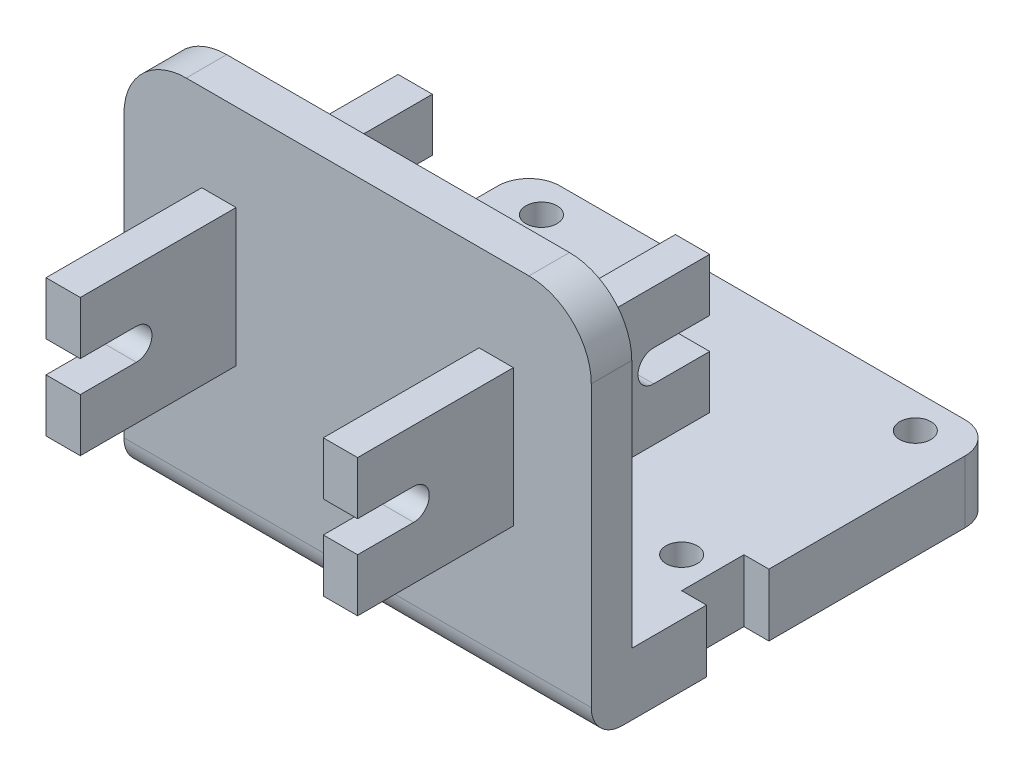
SolidWorks part; units mm, degrees
ref_plane "Front Plane" through (0, 0, 0) normal (0, 0, 1) x (1, 0, 0)
ref_plane "Top Plane" through (0, 0, 0) normal (0, 1, 0) x (1, 0, 0)
ref_plane "Right Plane" through (0, 0, 0) normal (1, 0, 0) x (0, 0, -1)
sketch "Sketch1" plane through (0, 0, 0) normal (0, 1, 0) x (1, 0, 0)
  line L1 (-37.5, -27.5) -> (37.5, -27.5)
  line L2 (-37.5, -27.5) -> (-37.5, 27.5)
  line L3 (-37.5, 27.5) -> (37.5, 27.5)
  line L4 (37.5, -27.5) -> (37.5, 27.5)
  line L5 (-37.5, -27.5) -> (37.5, 27.5) construction
  line L6 (-37.5, 27.5) -> (37.5, -27.5) construction
  circle A0 centre (-30, 22) radius 2.5
  circle A1 centre (30, 22) radius 2.5
  circle A2 centre (0, -16.5) radius 2.5
  point P0 (0, 0)
  dimension "D3" = 5
  dimension "D4" = 5
  dimension "D5" = 5
  dimension "D1" = 75
  dimension "D2" = 55
  dimension "D6" = 7.5
  dimension "D7" = 7.5
  dimension "D8" = 30
  dimension "D9" = 38.5
extrude "Boss-Extrude1" add sketch "Sketch1" along normal blind 10 contours L3 L4 L1 L2
sketch "Sketch7" plane through (0, 0, 0) normal (0, 1, 0) x (1, 0, 0)
  line L5 (-37.5, -27.5) -> (37.5, -27.5)
  line L6 (-37.5, -27.5) -> (-37.5, -37.5)
  line L7 (-37.5, -37.5) -> (37.5, -37.5)
  line L8 (37.5, -27.5) -> (37.5, -37.5)
  dimension "D1" = 10
  dimension "D2" = 75
extrude "Boss-Extrude2" add sketch "Sketch7" along normal blind 60
sketch "Sketch9" plane through (0, 60, 0) normal (0, 1, 0) x (1, 0, 0)
  line L0 (37.5, -37.5) -> (37.5, -27.5) construction
  line L1 (-37.5, -27.5) -> (37.5, -27.5)
  line L2 (-37.5, -27.5) -> (-37.5, -31)
  line L3 (-37.5, -31) -> (37.5, -31)
  line L4 (37.5, -27.5) -> (37.5, -31)
  dimension "D1" = 3.5
extrude "Cut-Extrude5" cut sketch "Sketch9" against normal blind 50
fillet "Fillet3" radius 5 1 edges at (0, 0, 37.5)
fillet "Fillet4" radius 5 2 edges at (37.5, 5, -27.5) (-37.5, 5, -27.5)
sketch "Sketch10" plane through (0, 0, 37.5) normal (0, 0, 1) x (1, 0, 0)
  line L1 (-23, 50) -> (23, 50)
  line L2 (-23, 50) -> (-23, 20)
  line L3 (-23, 20) -> (23, 20)
  line L4 (23, 50) -> (23, 20)
  line L5 (-37.5, 60) -> (-37.5, 5) construction
  line L6 (-37.5, 60) -> (37.5, 60) construction
  point P6 (0, 50)
  dimension "D1" = 30
  dimension "D2" = 46
  dimension "D3" = 37.5
  dimension "D4" = 10
extrude "Boss-Extrude3" add sketch "Sketch10" along normal blind 21
sketch "Sketch11" plane through (0, 50, 0) normal (0, 1, 0) x (1, 0, 0)
  line L0 (-37.5, -37.5) -> (37.5, -37.5) construction
  line L1 (-18, -37.5) -> (18, -37.5)
  line L2 (-18, -37.5) -> (-18, -53.5)
  line L3 (-18, -53.5) -> (18, -53.5)
  line L4 (18, -37.5) -> (18, -53.5)
  line L5 (-23, -58.5) -> (-23, -37.5) construction
  point P6 (0, -37.5)
  dimension "D1" = 36
  dimension "D2" = 23
  dimension "D3" = 16
extrude "Cut-Extrude6" cut sketch "Sketch11" against normal through all
sketch "Sketch12" plane through (0, 0, 31) normal (0, 0, -1) x (-1, 0, 0)
  line L1 (-23, 50) -> (23, 50)
  line L2 (-23, 50) -> (-23, 20)
  line L3 (-23, 20) -> (23, 20)
  line L4 (23, 50) -> (23, 20)
  line L6 (37.5, 60) -> (-37.5, 60) construction
  line L8 (-37.5, 10) -> (-37.5, 60) construction
  point P8 (0, 50)
  dimension "D1" = 46
  dimension "D2" = 30
  dimension "D3" = 10
  dimension "D4" = 37.5
extrude "Boss-Extrude4" add sketch "Sketch12" along normal blind 21
sketch "Sketch14" plane through (0, 50, 0) normal (0, 1, 0) x (1, 0, 0)
  line L0 (-23, -31) -> (23, -31) construction
  line L1 (-18, -31) -> (18, -31)
  line L2 (-18, -31) -> (-18, -15)
  line L3 (-18, -15) -> (18, -15)
  line L4 (18, -31) -> (18, -15)
  line L5 (-23, -10) -> (-23, -31) construction
  dimension "D1" = 36
  dimension "D2" = 5
  dimension "D3" = 16
extrude "Cut-Extrude7" cut sketch "Sketch14" against normal up to next
sketch "Sketch16" plane through (0, 50, 0) normal (0, 1, 0) x (1, 0, 0)
  line L0 (-19.5, -31) -> (-19.5, -12.8854)
  line L1 (-23, -31) -> (-18, -31) construction
  line L2 (-19.5, -12.8854) -> (-19.5, -10)
  line L3 (-23, -10) -> (23, -10) construction
  line L4 (-19.5, -10) -> (19.5, -9.8969)
  line L5 (19.5, -9.8969) -> (19.5, -31)
  line L6 (23, -10) -> (23, -31) construction
  line L7 (19.5, -31) -> (-19.5, -31)
  line L8 (-23, -10) -> (-23, -31) construction
  line L9 (-33.2343, -34.25) -> (29.1707, -34.25)
  line L10 (-37.5, -31) -> (37.5, -31) construction
  line L14 (19.5, -58.6031) -> (19.5, -37.5)
  line L15 (-19.5, -58.5) -> (19.5, -58.6031)
  line L16 (-19.5, -55.6146) -> (-19.5, -58.5)
  line L17 (-19.5, -37.5) -> (-19.5, -55.6146)
  line L18 (19.5, -37.5) -> (-19.5, -37.5)
  dimension "D1" = 3.5
  dimension "D2" = 21.1031
  dimension "D3" = 3.5
  dimension "D4" = 3.25
extrude "Cut-Extrude9" cut sketch "Sketch16" along direction (0, -1, 0) on the side against the normal up to next (30 mm away) contours L14 L18 L17 L16 L15 | L7 L0 L2 L4 L5
sketch "Sketch17" plane through (-23, 0, 0) normal (-1, 0, 0) x (0, 0, 1)
  line L0 (10, 24) -> (31, 24)
  line L1 (10, 20) -> (10, 50) construction
  line L2 (31, 20) -> (31, 50) construction
  line L3 (10, 46) -> (31, 46)
  line L4 (10, 50) -> (31, 50) construction
  line L5 (10, 20) -> (31, 20) construction
  line L6 (15, 37.5) -> (10, 37.5)
  line L7 (15, 32.5) -> (10, 32.5)
  line L8 (10, 37.5) -> (10, 32.5)
  line L9 (10, 46) -> (10, 50)
  line L10 (10, 50) -> (31, 50)
  line L11 (31, 10) -> (31, 60) construction
  line L12 (10, 50) -> (31, 50) construction
  line L13 (31, 50) -> (31, 46)
  line L14 (31, 24) -> (31, 20)
  line L15 (31, 20) -> (10, 20)
  line L16 (10, 20) -> (10, 24)
  line L17 (34.25, 60) -> (34.25, 0)
  line L18 (37.5, 60) -> (31, 60) construction
  line L19 (37.5, 24) -> (37.5, 20)
  line L20 (37.5, 20) -> (58.5, 20)
  line L21 (58.5, 20) -> (58.5, 24)
  line L22 (58.5, 24) -> (37.5, 24)
  line L23 (58.5, 37.5) -> (58.5, 32.5)
  line L24 (53.5, 32.5) -> (58.5, 32.5)
  line L25 (53.5, 37.5) -> (58.5, 37.5)
  line L26 (58.5, 46) -> (58.5, 50)
  line L27 (58.5, 50) -> (37.5, 50)
  line L28 (37.5, 50) -> (37.5, 46)
  line L29 (58.5, 46) -> (37.5, 46)
  arc A0 (15, 32.5) -> (15, 37.5) centre (15, 35) ccw
  arc A1 (53.5, 32.5) -> (53.5, 37.5) centre (53.5, 35) cw
  line M14 (31, 20) -> (31, 50)
  line M15 (31, 50) -> (10, 50)
  line M16 (10, 50) -> (10, 20)
  line M17 (10, 20) -> (31, 20)
  dimension "D3" = 5
  dimension "D1" = 4
  dimension "D2" = 4
  dimension "D4" = 5
  dimension "D5" = 15
extrude "Cut-Extrude10" cut sketch "Sketch17" against normal through all contours L29 L26 L27 L28 | A1 L24 L23 L25 | L21 L22 L19 L20 | L3 M16 M14 M15 | L7 A0 L6 M16 | L0 M16 M17 M14
sketch "Sketch18" plane through (-23, 0, 0) normal (-1, 0, 0) x (0, 0, 1)
  line L7 (31, 24) -> (31, 46)
  line L8 (31, 46) -> (10, 46)
  line L9 (10, 46) -> (10, 37.5)
  line L10 (10, 37.5) -> (15, 37.5)
  line L11 (15, 32.5) -> (10, 32.5)
  line L12 (10, 32.5) -> (10, 24)
  line L13 (10, 24) -> (31, 24)
  line L14 (31, 24) -> (31, 46)
  line L15 (31, 46) -> (10, 46)
  line L16 (10, 46) -> (10, 37.5)
  line L17 (10, 37.5) -> (15, 37.5)
  line L18 (15, 32.5) -> (10, 32.5)
  line L19 (10, 32.5) -> (10, 24)
  line L20 (10, 24) -> (31, 24)
  arc A1 (15, 32.5) -> (15, 37.5) centre (15, 35) ccw
  arc A2 (15, 32.5) -> (15, 37.5) centre (15, 35) ccw
  dimension "D1" = 0
extrude "Boss-Extrude5" add sketch "Sketch18" along normal blind 2
sketch "Sketch19" plane through (23, 0, 0) normal (1, 0, 0) x (0, 0, -1)
  line L7 (-10, 37.5) -> (-10, 46)
  line L8 (-10, 46) -> (-31, 46)
  line L9 (-31, 46) -> (-31, 24)
  line L10 (-31, 24) -> (-10, 24)
  line L11 (-10, 24) -> (-10, 32.5)
  line L12 (-10, 32.5) -> (-15, 32.5)
  line L13 (-15, 37.5) -> (-10, 37.5)
  line L14 (-10, 37.5) -> (-10, 46)
  line L15 (-10, 46) -> (-31, 46)
  line L16 (-31, 46) -> (-31, 24)
  line L17 (-31, 24) -> (-10, 24)
  line L18 (-10, 24) -> (-10, 32.5)
  line L19 (-10, 32.5) -> (-15, 32.5)
  line L20 (-15, 37.5) -> (-10, 37.5)
  arc A1 (-15, 37.5) -> (-15, 32.5) centre (-15, 35) ccw
  arc A2 (-15, 37.5) -> (-15, 32.5) centre (-15, 35) ccw
  dimension "D1" = 0
extrude "Boss-Extrude6" add sketch "Sketch19" along normal blind 2
sketch "Sketch20" plane through (-23, 0, 0) normal (-1, 0, 0) x (0, 0, 1)
  line L7 (53.5, 37.5) -> (58.5, 37.5)
  line L8 (58.5, 37.5) -> (58.5, 46)
  line L9 (58.5, 46) -> (37.5, 46)
  line L10 (37.5, 46) -> (37.5, 24)
  line L11 (37.5, 24) -> (58.5, 24)
  line L12 (58.5, 24) -> (58.5, 32.5)
  line L13 (58.5, 32.5) -> (53.5, 32.5)
  line L14 (53.5, 37.5) -> (58.5, 37.5)
  line L15 (58.5, 37.5) -> (58.5, 46)
  line L16 (58.5, 46) -> (37.5, 46)
  line L17 (37.5, 46) -> (37.5, 24)
  line L18 (37.5, 24) -> (58.5, 24)
  line L19 (58.5, 24) -> (58.5, 32.5)
  line L20 (58.5, 32.5) -> (53.5, 32.5)
  arc A1 (53.5, 37.5) -> (53.5, 32.5) centre (53.5, 35) ccw
  arc A2 (53.5, 37.5) -> (53.5, 32.5) centre (53.5, 35) ccw
  dimension "D1" = 0
extrude "Boss-Extrude7" add sketch "Sketch20" along normal blind 2
sketch "Sketch21" plane through (23, 0, 0) normal (1, 0, 0) x (0, 0, -1)
  line L7 (-58.5, 37.5) -> (-53.5, 37.5)
  line L8 (-53.5, 32.5) -> (-58.5, 32.5)
  line L9 (-58.5, 32.5) -> (-58.5, 24)
  line L10 (-58.5, 24) -> (-37.5, 24)
  line L11 (-37.5, 24) -> (-37.5, 46)
  line L12 (-37.5, 46) -> (-58.5, 46)
  line L13 (-58.5, 46) -> (-58.5, 37.5)
  line L14 (-58.5, 37.5) -> (-53.5, 37.5)
  line L15 (-53.5, 32.5) -> (-58.5, 32.5)
  line L16 (-58.5, 32.5) -> (-58.5, 24)
  line L17 (-58.5, 24) -> (-37.5, 24)
  line L18 (-37.5, 24) -> (-37.5, 46)
  line L19 (-37.5, 46) -> (-58.5, 46)
  line L20 (-58.5, 46) -> (-58.5, 37.5)
  arc A1 (-53.5, 32.5) -> (-53.5, 37.5) centre (-53.5, 35) ccw
  arc A2 (-53.5, 32.5) -> (-53.5, 37.5) centre (-53.5, 35) ccw
  dimension "D1" = 0
extrude "Boss-Extrude8" add sketch "Sketch21" along normal blind 2
sketch "Sketch22" plane through (0, 0, 10) normal (0, 0, -1) x (-1, 0, 0)
  line L0 (19.5, 24) -> (25, 24) construction
  line L1 (25, 24) -> (25, 32.5) construction
  line L2 (25, 32.5) -> (19.5, 32.5) construction
  line L3 (19.5, 32.5) -> (19.5, 24) construction
  line L4 (25, 46) -> (19.5, 46) construction
  line L5 (19.5, 46) -> (19.5, 37.5) construction
  line L6 (19.5, 37.5) -> (25, 37.5) construction
  line L7 (25, 37.5) -> (25, 46) construction
  line L8 (-19.5, 24) -> (-19.5, 32.5) construction
  line L9 (-19.5, 32.5) -> (-25, 32.5) construction
  line L10 (-25, 32.5) -> (-25, 24) construction
  line L11 (-25, 24) -> (-19.5, 24) construction
  line L12 (-19.5, 46) -> (-25, 46) construction
  line L13 (-25, 46) -> (-25, 37.5) construction
  line L14 (-25, 37.5) -> (-19.5, 37.5) construction
  line L15 (-19.5, 37.5) -> (-19.5, 46) construction
  line L16 (19.5, 24) -> (25, 24)
  line L17 (25, 24) -> (25, 32.5)
  line L18 (25, 32.5) -> (19.5, 32.5)
  line L19 (19.5, 32.5) -> (19.5, 24)
  line L20 (25, 46) -> (19.5, 46)
  line L21 (19.5, 46) -> (19.5, 37.5)
  line L22 (19.5, 37.5) -> (25, 37.5)
  line L23 (25, 37.5) -> (25, 46)
  line L24 (-19.5, 24) -> (-19.5, 32.5)
  line L25 (-19.5, 32.5) -> (-25, 32.5)
  line L26 (-25, 32.5) -> (-25, 24)
  line L27 (-25, 24) -> (-19.5, 24)
  line L28 (-19.5, 46) -> (-25, 46)
  line L29 (-25, 46) -> (-25, 37.5)
  line L30 (-25, 37.5) -> (-19.5, 37.5)
  line L31 (-19.5, 37.5) -> (-19.5, 46)
extrude "Boss-Extrude9" add sketch "Sketch22" along normal blind 4
sketch "Sketch23" plane through (0, 0, 58.5) normal (0, 0, 1) x (1, 0, 0)
  line L0 (25, 32.5) -> (19.5, 32.5) construction
  line L1 (19.5, 32.5) -> (19.5, 24) construction
  line L2 (19.5, 24) -> (25, 24) construction
  line L3 (25, 24) -> (25, 32.5) construction
  line L4 (19.5, 46) -> (19.5, 37.5) construction
  line L5 (19.5, 37.5) -> (25, 37.5) construction
  line L6 (25, 37.5) -> (25, 46) construction
  line L7 (25, 46) -> (19.5, 46) construction
  line L8 (-19.5, 32.5) -> (-25, 32.5) construction
  line L9 (-25, 32.5) -> (-25, 24) construction
  line L10 (-25, 24) -> (-19.5, 24) construction
  line L11 (-19.5, 24) -> (-19.5, 32.5) construction
  line L12 (-19.5, 46) -> (-25, 46) construction
  line L13 (-25, 46) -> (-25, 37.5) construction
  line L14 (-25, 37.5) -> (-19.5, 37.5) construction
  line L15 (-19.5, 37.5) -> (-19.5, 46) construction
  line L16 (25, 32.5) -> (19.5, 32.5)
  line L17 (19.5, 32.5) -> (19.5, 24)
  line L18 (19.5, 24) -> (25, 24)
  line L19 (25, 24) -> (25, 32.5)
  line L20 (19.5, 46) -> (19.5, 37.5)
  line L21 (19.5, 37.5) -> (25, 37.5)
  line L22 (25, 37.5) -> (25, 46)
  line L23 (25, 46) -> (19.5, 46)
  line L24 (-19.5, 32.5) -> (-25, 32.5)
  line L25 (-25, 32.5) -> (-25, 24)
  line L26 (-25, 24) -> (-19.5, 24)
  line L27 (-19.5, 24) -> (-19.5, 32.5)
  line L28 (-19.5, 46) -> (-25, 46)
  line L29 (-25, 46) -> (-25, 37.5)
  line L30 (-25, 37.5) -> (-19.5, 37.5)
  line L31 (-19.5, 37.5) -> (-19.5, 46)
extrude "Boss-Extrude10" add sketch "Sketch23" along normal blind 4
fillet "Fillet5" radius 10 2 edges at (37.5, 60, 34.25) (-37.5, 60, 34.25)
sketch "Sketch25" plane through (0, 10, 0) normal (0, 1, 0) x (1, 0, 0)
  line L0 (-37.5, -27.5) -> (-37.5, 27.5) construction
  line L1 (-37.5, -15) -> (-33.5, -15)
  line L2 (-37.5, -15) -> (-37.5, -19)
  line L3 (-37.5, -19) -> (-33.5, -19)
  line L4 (-33.5, -15) -> (-33.5, -19)
  line L5 (-37.5, 22.5) -> (-37.5, -31) construction
  line L6 (-37.5, -9) -> (-33.5, -9)
  line L7 (-37.5, -9) -> (-37.5, -13)
  line L8 (-37.5, -13) -> (-33.5, -13)
  line L9 (-33.5, -9) -> (-33.5, -13)
  line L10 (-37.5, -31) -> (37.5, -31) construction
  line L11 (0, -16.5) -> (0, 15.2901)
  line L12 (-37.5, -13) -> (-33.5, -13)
  line L13 (-37.5, -13) -> (-37.5, -15)
  line L14 (-37.5, -15) -> (-33.5, -15)
  line L15 (-33.5, -13) -> (-33.5, -15)
  line L16 (33.5, -13) -> (33.5, -15)
  line L17 (37.5, -15) -> (33.5, -15)
  line L18 (37.5, -13) -> (37.5, -15)
  line L19 (37.5, -13) -> (33.5, -13)
  line L20 (33.5, -9) -> (33.5, -13)
  line L21 (37.5, -13) -> (33.5, -13)
  line L22 (37.5, -9) -> (37.5, -13)
  line L23 (33.5, -15) -> (33.5, -19)
  line L24 (37.5, -19) -> (33.5, -19)
  line L25 (37.5, -15) -> (37.5, -19)
  line L26 (37.5, -15) -> (33.5, -15)
  line L27 (37.5, -9) -> (33.5, -9)
  line M8 (37.5, -31) -> (37.5, 22.5)
  line M12 (-37.5, 22.5) -> (-37.5, -31)
  dimension "D1" = 4
  dimension "D2" = 4
  dimension "D3" = 2
  dimension "D4" = 12
  dimension "D6" = 4
extrude "Cut-Extrude11" cut sketch "Sketch25" against normal through all contours L9 L6 L8 M12 | L15 L8 L1 M12 | L4 L1 L3 M12 | L27 L20 L19 M8 | L19 L16 L17 M8 | L24 L17 L23 M8
sketch "Sketch27" plane through (0, 10, 0) normal (0, 1, 0) x (1, 0, 0)
  line L0 (0, -16.5) -> (0, -8.3412)
  line L1 (-33.5, -9) -> (-23.5, -9)
  line L2 (-33.5, -9) -> (-33.5, -19)
  line L3 (-33.5, -19) -> (-23.5, -19)
  line L4 (-23.5, -9) -> (-23.5, -19)
  circle A0 centre (-28.5, -14) radius 2.5
  circle A1 centre (28.5, -14) radius 2.5
  dimension "D3" = 5
  dimension "D1" = 10
  dimension "D2" = 10
  dimension "D4" = 5
  dimension "D5" = 5
extrude "Cut-Extrude14" cut sketch "Sketch27" against normal through all contours A0 | A1
